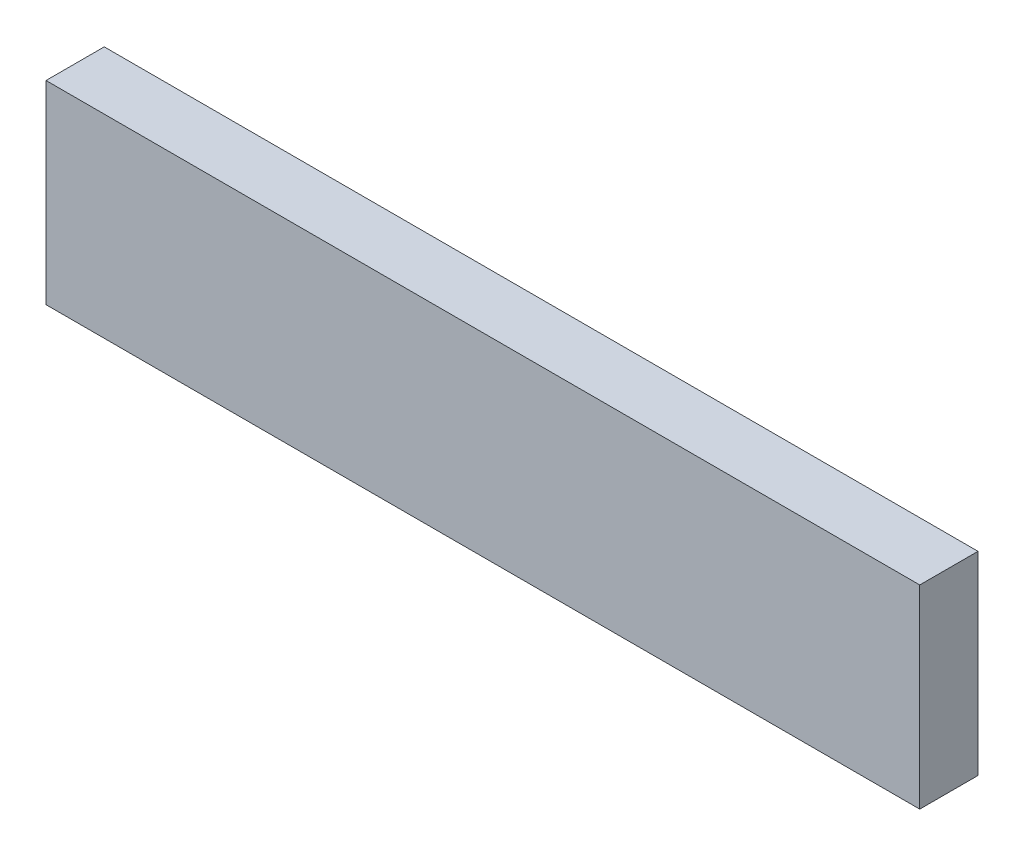
SolidWorks part; units mm, degrees
ref_plane "Front Plane" through (0, 0, 0) normal (0, 0, 1) x (1, 0, 0)
ref_plane "Top Plane" through (0, 0, 0) normal (0, 1, 0) x (1, 0, 0)
ref_plane "Right Plane" through (0, 0, 0) normal (1, 0, 0) x (0, 0, -1)
sketch "Sketch1" plane through (0, 0, 0) normal (0, 0, 1) x (1, 0, 0)
  line L1 (22.5, -5) -> (-22.5, -5)
  line L2 (22.5, -5) -> (22.5, 5)
  line L3 (22.5, 5) -> (-22.5, 5)
  line L4 (-22.5, -5) -> (-22.5, 5)
  line L5 (22.5, -5) -> (-22.5, 5) construction
  line L6 (22.5, 5) -> (-22.5, -5) construction
  point P0 (0, 0)
  dimension "D1" = 10
  dimension "D2" = 45
extrude "Boss-Extrude1" add sketch "Sketch1" along normal blind 3
sketch "Sketch2" plane through (22.5, 0, 0) normal (1, 0, 0) x (0, 0, -1)
  line L0 (0, -5) -> (0, 5) construction
  point P0 (0, 0)
